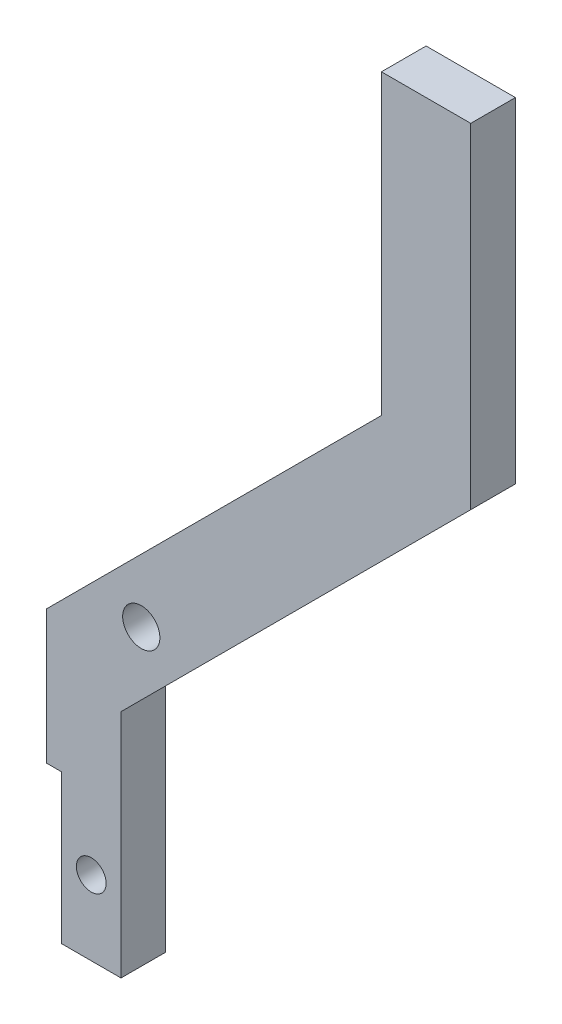
SolidWorks part; units mm, degrees
material "Malleable Cast Iron"
ref_plane "Front Plane" through (0, 0, 0) normal (0, 0, 1) x (1, 0, 0)
ref_plane "Top Plane" through (0, 0, 0) normal (0, 1, 0) x (1, 0, 0)
ref_plane "Right Plane" through (0, 0, 0) normal (1, 0, 0) x (0, 0, -1)
sketch "Sketch1" plane through (0, 0, 0) normal (0, 0, 1) x (1, 0, 0)
  line L0 (-29.184, -29.9692) -> (-29.184, -14.4692)
  line L1 (-29.184, -29.9692) -> (-35.184, -29.9692)
  line L2 (-11.684, 11.5161) -> (-11.684, 31.5161)
  line L3 (-11.684, 31.5161) -> (-5.684, 31.5161)
  line L4 (-35.184, -29.9692) -> (-35.184, -11.9839)
  line L5 (-5.684, 31.5161) -> (-5.684, 9.0308)
  line L6 (-29.184, -14.4692) -> (-5.684, 9.0308)
  line L7 (-11.684, 11.5161) -> (-35.184, -11.9839)
  line L8 (-35.184, -11.9839) -> (54.4833, -11.9839) construction
  dimension "D1" = 17.5
  dimension "D2" = 45
  dimension "D3" = 20
  dimension "D4" = 15.5
  dimension "D5" = 6
  dimension "D6" = 6
  dimension "D7" = 6
extrude "Boss-Extrude1" add sketch "Sketch1" along normal blind 3
sketch "Sketch3" plane through (0, 0, 3) normal (0, 0, 1) x (1, 0, 0)
  line L2 (-35.184, -29.9692) -> (-33.184, -29.9692)
  line L3 (-35.184, -29.9692) -> (-35.184, -19.9692)
  line L5 (-35.184, -19.9692) -> (-33.184, -19.9692)
  line L6 (-33.184, -29.9692) -> (-33.184, -19.9692)
  dimension "D1" = 10
  dimension "D2" = 2
extrude "Cut-Extrude2" cut sketch "Sketch3" against normal blind 3
sketch "Sketch5" plane through (0, 0, 3) normal (0, 0, 1) x (1, 0, 0)
  line L1 (-35.184, -19.9692) -> (-34.184, -19.9692)
  line L2 (-35.184, -19.9692) -> (-35.184, -7.8649)
  line L3 (-35.184, -7.8649) -> (-34.184, -7.8649)
  line L4 (-34.184, -19.9692) -> (-34.184, -7.8649)
  dimension "D1" = 1
extrude "Cut-Extrude4" cut sketch "Sketch5" against normal blind 10
sketch "Sketch6" plane through (0, 0, 3) normal (0, 0, 1) x (1, 0, 0)
  line L0 (-34.184, -19.9692) -> (-34.184, -10.9839) construction
  line L1 (-11.684, 11.5161) -> (-34.184, -10.9839) construction
  circle A0 centre (-27.824, -8.8666) radius 1.25
  point P0 (-27.824, -8.8666)
  dimension "D1" = 6.36
  dimension "D2" = 3
extrude "Cut-Extrude5" cut sketch "Sketch6" against normal blind 3
sketch "Sketch7" plane through (0, 0, 3) normal (0, 0, 1) x (1, 0, 0)
  circle A0 centre (-31.184, -24.9692) radius 1
extrude "Cut-Extrude6" cut sketch "Sketch7" against normal blind 10
